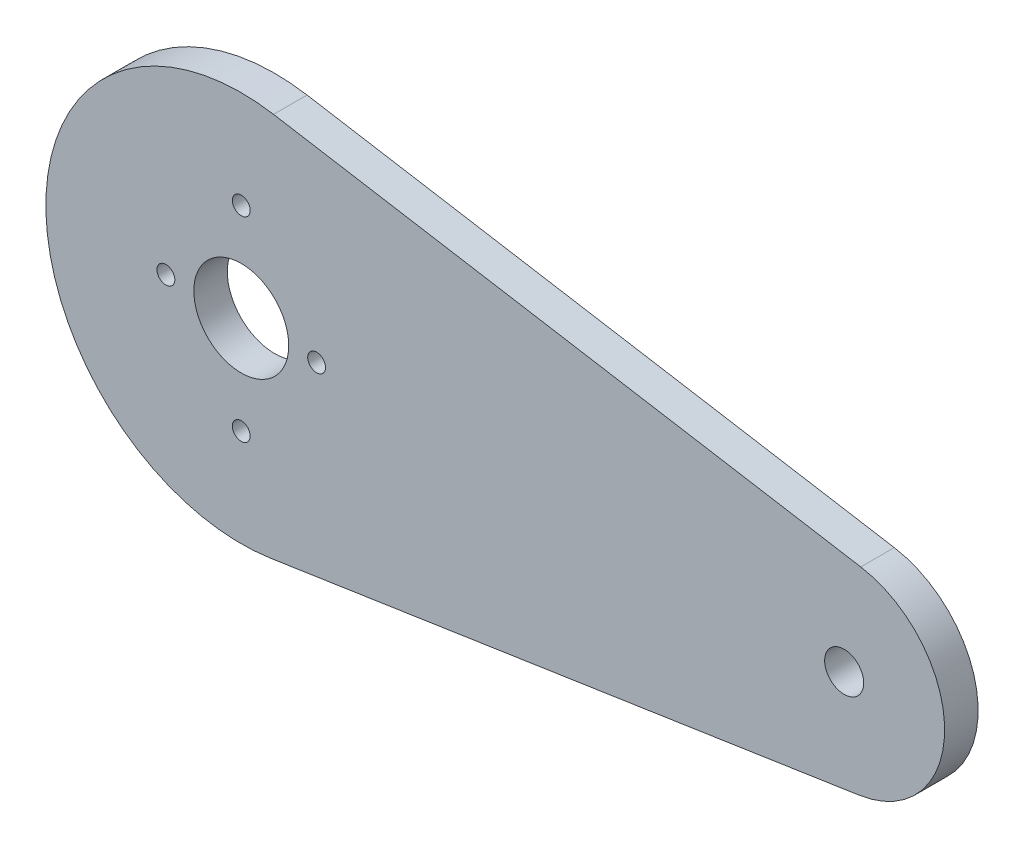
SolidWorks part; units mm, degrees
ref_plane "Front Plane" through (0, 0, 0) normal (0, 0, 1) x (1, 0, 0)
ref_plane "Top Plane" through (0, 0, 0) normal (0, 1, 0) x (1, 0, 0)
ref_plane "Right Plane" through (0, 0, 0) normal (1, 0, 0) x (0, 0, -1)
sketch "Sketch1" plane through (0, 0, 0) normal (0, 0, 1) x (1, 0, 0)
  line L0 (-20.22, 57.58) -> (33.7783, 57.1554) construction
  line L1 (-20.22, 57.58) -> (33.7783, 57.1554) construction
  line L2 (-17.3296, 74.8396) -> (35.2648, 66.0318)
  line L3 (-17.6013, 40.277) -> (35.1251, 48.2567)
  circle A0 centre (-20.22, 57.58) radius 17.5 construction
  circle A1 centre (-20.22, 57.58) radius 17.5 construction
  circle A2 centre (33.7783, 57.1554) radius 9 construction
  arc A3 (-17.3296, 74.8396) -> (-17.6013, 40.277) centre (-20.22, 57.58) ccw
  arc A4 (35.2648, 66.0318) -> (35.1251, 48.2567) centre (33.7783, 57.1554) cw
  circle A5 centre (33.7783, 57.1554) radius 1.75
  circle A6 centre (-20.22, 57.58) radius 4.25
  circle A7 centre (-13.47, 57.5269) radius 0.8
  circle A8 centre (-26.97, 57.58) radius 0.8
  circle A9 centre (-20.22, 66.33) radius 0.8
  circle A10 centre (-20.22, 48.83) radius 0.8
  dimension "D1" = 18
  dimension "D2" = 3.5
  dimension "D3" = 8.5
  dimension "D4" = 1.6
  dimension "D5" = 8.75
  dimension "D6" = 6.75
  dimension "D7" = 6.75
  dimension "D8" = 8.75
extrude "Boss-Extrude2" add sketch "Sketch1" against normal blind 3
